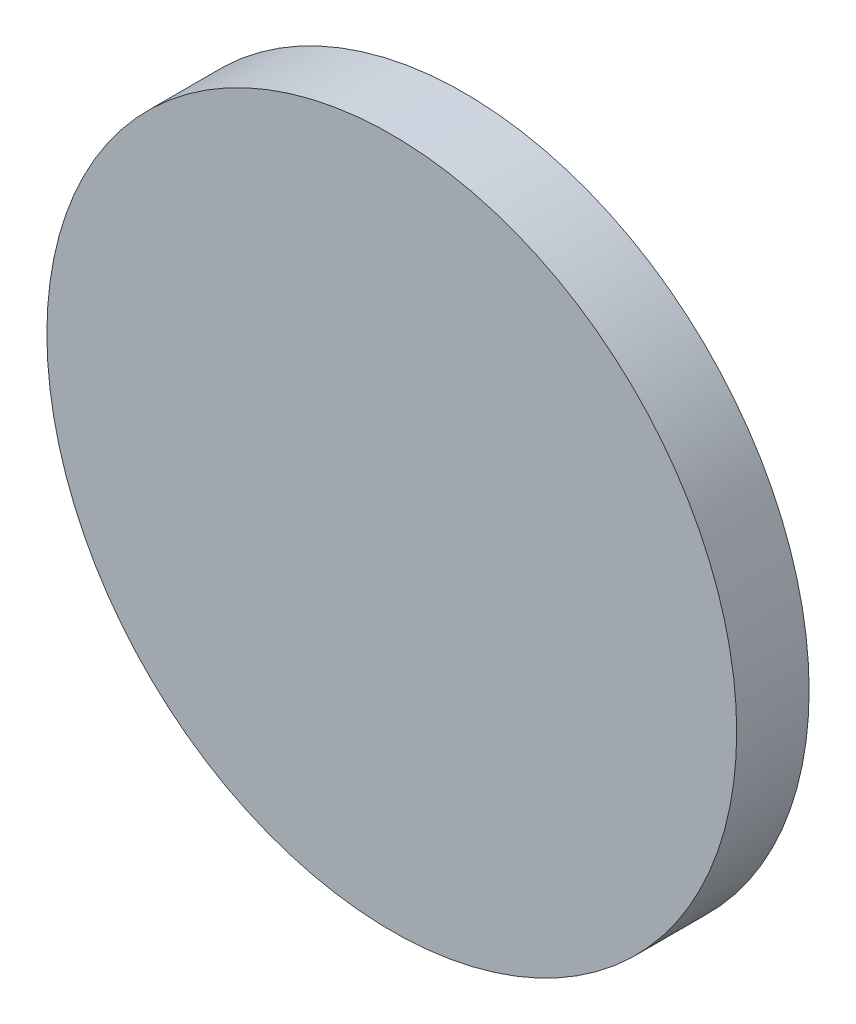
SolidWorks part; units mm, degrees
ref_plane "前视基准面" through (0, 0, 0) normal (0, 0, 1) x (1, 0, 0)
ref_plane "上视基准面" through (0, 0, 0) normal (0, 1, 0) x (1, 0, 0)
ref_plane "右视基准面" through (0, 0, 0) normal (1, 0, 0) x (0, 0, -1)
sketch "草图1" plane through (0, 0, 0) normal (0, 0, 1) x (1, 0, 0)
  circle A0 centre (0, 0) radius 19.05
  dimension "D1" = 38.1
extrude "凸台-拉伸1" add sketch "草图1" along normal blind 4 contours A0
